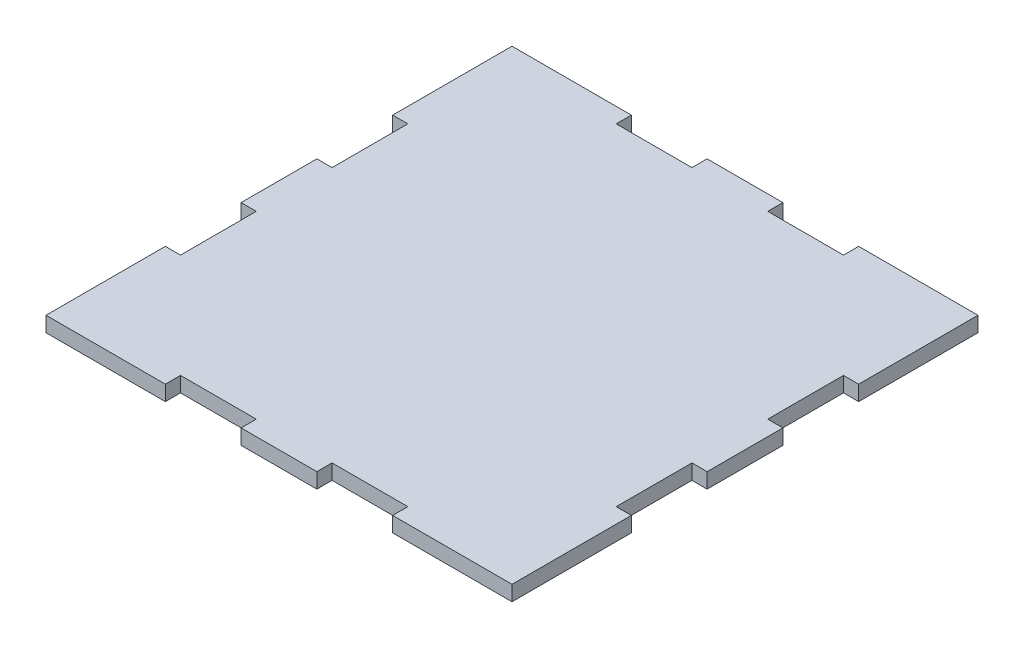
SolidWorks part; units mm, degrees
ref_plane "Спереди" through (0, 0, 0) normal (0, 0, 1) x (1, 0, 0)
ref_plane "Сверху" through (0, 0, 0) normal (0, 1, 0) x (1, 0, 0)
ref_plane "Справа" through (0, 0, 0) normal (1, 0, 0) x (0, 0, -1)
sketch "Эскиз1" plane through (0, 0, 0) normal (0, 1, 0) x (1, 0, 0)
  line L0 (31.5, 0) -> (31.5, 4)
  line L1 (0, 0) -> (31.5, 0)
  line L2 (0, 0) -> (0, 31.5)
  line L3 (0, 123) -> (31.5, 123)
  line L4 (123, 0) -> (123, 31.5)
  line L5 (31.5, 4) -> (51.5, 4)
  line L6 (51.5, 4) -> (51.5, 0)
  line L7 (71.5, 0) -> (71.5, 4)
  line L8 (71.5, 4) -> (91.5, 4)
  line L9 (91.5, 4) -> (91.5, 0)
  line L10 (51.5, 0) -> (71.5, 0)
  line L11 (91.5, 0) -> (123, 0)
  line L12 (0, 0) -> (123, 123) construction
  line L13 (0, 123) -> (123, 0) construction
  line L14 (0, 91.5) -> (4, 91.5)
  line L15 (4, 91.5) -> (4, 71.5)
  line L16 (4, 71.5) -> (0, 71.5)
  line L17 (0, 51.5) -> (4, 51.5)
  line L18 (4, 51.5) -> (4, 31.5)
  line L19 (4, 31.5) -> (0, 31.5)
  line L20 (91.5, 123) -> (91.5, 119)
  line L21 (91.5, 119) -> (71.5, 119)
  line L22 (71.5, 119) -> (71.5, 123)
  line L23 (51.5, 123) -> (51.5, 119)
  line L24 (51.5, 119) -> (31.5, 119)
  line L25 (31.5, 119) -> (31.5, 123)
  line L26 (123, 31.5) -> (119, 31.5)
  line L27 (119, 31.5) -> (119, 51.5)
  line L28 (119, 51.5) -> (123, 51.5)
  line L29 (123, 71.5) -> (119, 71.5)
  line L30 (119, 71.5) -> (119, 91.5)
  line L31 (119, 91.5) -> (123, 91.5)
  line L32 (51.5, 123) -> (71.5, 123)
  line L33 (91.5, 123) -> (123, 123)
  line L34 (123, 91.5) -> (123, 123)
  line L35 (123, 51.5) -> (123, 71.5)
  line L36 (0, 51.5) -> (0, 71.5)
  line L37 (0, 91.5) -> (0, 123)
  line L38 (61.5, 0) -> (61.5, 61.5) construction
  point P7 (61.5, 61.5)
  point P41 (61.5, 61.5)
  dimension "D1" = 123
  dimension "D2" = 20
  dimension "D3" = 20
  dimension "D4" = 4
  dimension "D6" = 2
  dimension "D7" = 4
extrude "Бобышка-Вытянуть1" add sketch "Эскиз1" along normal blind 4
